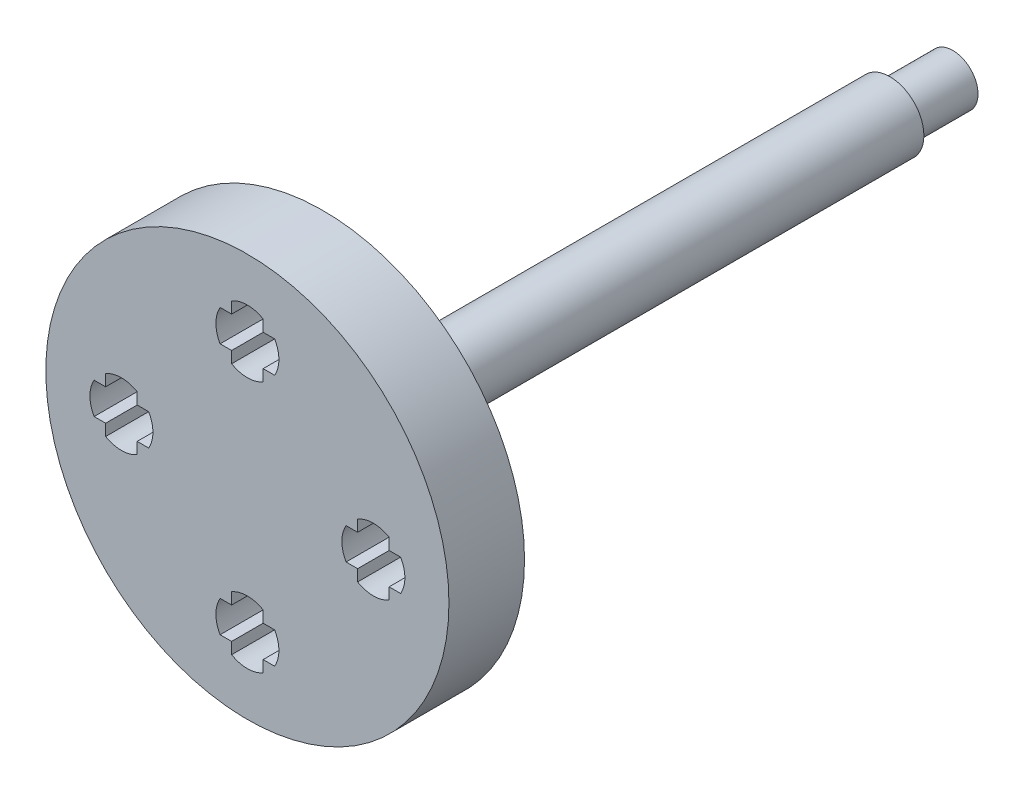
SolidWorks part; units mm, degrees
material "PLA"
ref_plane "Alzado" through (0, 0, 0) normal (0, 0, 1) x (1, 0, 0)
ref_plane "Planta" through (0, 0, 0) normal (0, 1, 0) x (1, 0, 0)
ref_plane "Vista lateral" through (0, 0, 0) normal (1, 0, 0) x (0, 0, -1)
sketch "Croquis2" plane through (0, 0, 0) normal (0, 0, 1) x (1, 0, 0)
  line L0 (0, 10) -> (0, 12.5) construction
  line L2 (2.5, 10) -> (0, 10) construction
  line L3 (0, 11.25) -> (2.1651, 11.25) construction
  line L4 (1.25, 10) -> (1.25, 12.1651) construction
  line L5 (1.25, 12.1651) -> (1.25, 11.25)
  line L6 (1.25, 11.25) -> (2.1651, 11.25)
  line L7 (2.1651, 8.75) -> (1.25, 8.75)
  line L8 (1.25, 8.75) -> (1.25, 7.8349)
  line L9 (-1.25, 7.8349) -> (-1.25, 8.75)
  line L10 (-1.25, 8.75) -> (-2.1651, 8.75)
  line L11 (-2.1651, 11.25) -> (-1.25, 11.25)
  line L12 (-1.25, 11.25) -> (-1.25, 12.1651)
  line L13 (12.1651, -1.25) -> (11.25, -1.25)
  line L14 (11.25, -1.25) -> (11.25, -2.1651)
  line L15 (8.75, -2.1651) -> (8.75, -1.25)
  line L16 (8.75, -1.25) -> (7.8349, -1.25)
  line L17 (7.8349, 1.25) -> (8.75, 1.25)
  line L18 (8.75, 1.25) -> (8.75, 2.1651)
  line L19 (11.25, 2.1651) -> (11.25, 1.25)
  line L20 (11.25, 1.25) -> (12.1651, 1.25)
  line L21 (-1.25, -12.1651) -> (-1.25, -11.25)
  line L22 (-1.25, -11.25) -> (-2.1651, -11.25)
  line L23 (-2.1651, -8.75) -> (-1.25, -8.75)
  line L24 (-1.25, -8.75) -> (-1.25, -7.8349)
  line L25 (1.25, -7.8349) -> (1.25, -8.75)
  line L26 (1.25, -8.75) -> (2.1651, -8.75)
  line L27 (2.1651, -11.25) -> (1.25, -11.25)
  line L28 (1.25, -11.25) -> (1.25, -12.1651)
  line L29 (-12.1651, 1.25) -> (-11.25, 1.25)
  line L30 (-11.25, 1.25) -> (-11.25, 2.1651)
  line L31 (-8.75, 2.1651) -> (-8.75, 1.25)
  line L32 (-8.75, 1.25) -> (-7.8349, 1.25)
  line L33 (-7.8349, -1.25) -> (-8.75, -1.25)
  line L34 (-8.75, -1.25) -> (-8.75, -2.1651)
  line L35 (-11.25, -2.1651) -> (-11.25, -1.25)
  line L36 (-11.25, -1.25) -> (-12.1651, -1.25)
  circle A0 centre (0, 0) radius 16
  circle A1 centre (0, 0) radius 10 construction
  circle A2 centre (0, 10) radius 2.5 construction
  arc A3 (0, 12.5) -> (1.25, 12.1651) centre (0, 10) cw
  arc A4 (2.1651, 11.25) -> (2.5, 10) centre (0, 10) cw
  arc A5 (2.5, 10) -> (2.1651, 8.75) centre (0, 10) cw
  arc A6 (1.25, 7.8349) -> (0, 7.5) centre (0, 10) cw
  arc A7 (0, 7.5) -> (-1.25, 7.8349) centre (0, 10) cw
  arc A8 (-2.1651, 8.75) -> (-2.5, 10) centre (0, 10) cw
  arc A9 (-2.5, 10) -> (-2.1651, 11.25) centre (0, 10) cw
  arc A10 (-1.25, 12.1651) -> (0, 12.5) centre (0, 10) cw
  arc A11 (12.1651, 1.25) -> (12.5, 0) centre (10, 0) cw
  arc A12 (12.5, 0) -> (12.1651, -1.25) centre (10, 0) cw
  arc A13 (11.25, -2.1651) -> (10, -2.5) centre (10, 0) cw
  arc A14 (10, -2.5) -> (8.75, -2.1651) centre (10, 0) cw
  arc A15 (7.8349, -1.25) -> (7.5, 0) centre (10, 0) cw
  arc A16 (7.5, 0) -> (7.8349, 1.25) centre (10, 0) cw
  arc A17 (8.75, 2.1651) -> (10, 2.5) centre (10, 0) cw
  arc A18 (10, 2.5) -> (11.25, 2.1651) centre (10, 0) cw
  arc A19 (1.25, -12.1651) -> (0, -12.5) centre (0, -10) cw
  arc A20 (0, -12.5) -> (-1.25, -12.1651) centre (0, -10) cw
  arc A21 (-2.1651, -11.25) -> (-2.5, -10) centre (0, -10) cw
  arc A22 (-2.5, -10) -> (-2.1651, -8.75) centre (0, -10) cw
  arc A23 (-1.25, -7.8349) -> (0, -7.5) centre (0, -10) cw
  arc A24 (0, -7.5) -> (1.25, -7.8349) centre (0, -10) cw
  arc A25 (2.1651, -8.75) -> (2.5, -10) centre (0, -10) cw
  arc A26 (2.5, -10) -> (2.1651, -11.25) centre (0, -10) cw
  arc A27 (-12.1651, -1.25) -> (-12.5, 0) centre (-10, 0) cw
  arc A28 (-12.5, 0) -> (-12.1651, 1.25) centre (-10, 0) cw
  arc A29 (-11.25, 2.1651) -> (-10, 2.5) centre (-10, 0) cw
  arc A30 (-10, 2.5) -> (-8.75, 2.1651) centre (-10, 0) cw
  arc A31 (-7.8349, 1.25) -> (-7.5, 0) centre (-10, 0) cw
  arc A32 (-7.5, 0) -> (-7.8349, -1.25) centre (-10, 0) cw
  arc A33 (-8.75, -2.1651) -> (-10, -2.5) centre (-10, 0) cw
  arc A34 (-10, -2.5) -> (-11.25, -2.1651) centre (-10, 0) cw
  point P33 (0, 10)
  point P84 (0, 0)
  dimension "D1" = 4
  dimension "D2" = 4
extrude "Saliente-Extruir1" add sketch "Croquis2" along normal blind 6
sketch "Croquis3" plane through (0, 0, 0) normal (0, 0, -1) x (-1, 0, 0)
  circle A0 centre (0, 0) radius 2.7
extrude "Saliente-Extruir2" add sketch "Croquis3" along normal blind 50
sketch "Croquis4" plane through (0, 0, -50) normal (0, 0, -1) x (-1, 0, 0)
  circle A0 centre (0, 0) radius 2.7
  circle A1 centre (0, 0) radius 2
extrude "Cortar-Extruir1" cut sketch "Croquis4" against normal blind 5
